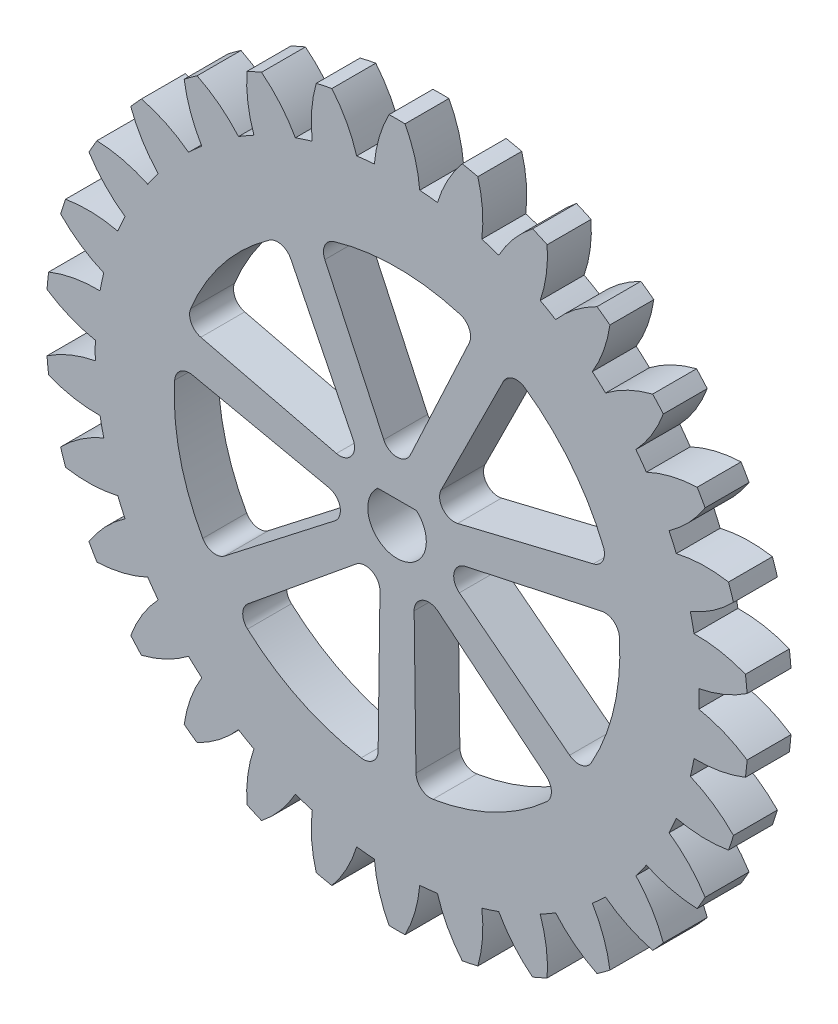
SolidWorks part; units mm, degrees
ref_plane "Front Plane" through (0, 0, 0) normal (0, 0, 1) x (1, 0, 0)
ref_plane "Top Plane" through (0, 0, 0) normal (0, 1, 0) x (1, 0, 0)
ref_plane "Right Plane" through (0, 0, 0) normal (1, 0, 0) x (0, 0, -1)
sketch "Sketch1" plane through (0, 0, 0) normal (0, 0, 1) x (1, 0, 0)
  circle A0 centre (0, 0) radius 24
  dimension "D1" = 48
extrude "Boss-Extrude1" add sketch "Sketch1" along normal blind 3
sketch "Sketch2" plane through (0, 0, 0) normal (0, 0, -1) x (-1, 0, 0)
  line L0 (0, 0) -> (0, 31.1786) construction
  line L1 (0, 0) -> (3.3147, 31.5373) construction
  line L2 (1.1781, 22.4691) -> (0, 22.4691) construction
  circle A0 centre (0, 0) radius 20.625 construction
  circle A1 centre (0, 0) radius 21.1431 construction
  circle A2 centre (0, 0) radius 22.5 construction
  arc A3 (1.5504, 20.5666) -> (2.7595, 20.4396) centre (0, 0) cw
  arc A4 (1.5504, 20.5666) -> (0.5461, 23.9938) centre (-7.4168, 19.7995) ccw
  circle A5 centre (0, 0) radius 24 construction
  arc A6 (2.7595, 20.4396) -> (4.4545, 23.583) centre (11.3713, 17.8248) cw
  arc A7 (0.5461, 23.9938) -> (4.4545, 23.583) centre (0, 0) cw
  dimension "D3" = 45
  dimension "D1" = 41.25
  dimension "D5" = 9
  dimension "D2" = 42.2862
  dimension "D4" = 6
  dimension "D6" = 1.1781
extrude "Cut-Extrude1" cut sketch "Sketch2" against normal through all
pattern_circular "CirPattern1" count 30 over 360 about axis through (0, 0, 0) along (0, 0, 1) of "Cut-Extrude1"
sketch "Sketch4" plane through (0, 0, 0) normal (0, 0, -1) x (-1, 0, 0)
  line L0 (0, 2.6286) -> (5.4036, 14.2321)
  line L1 (0, 2.6286) -> (-5.4036, 14.2321)
  line L2 (0, 0) -> (0, 15.2234) construction
  arc A1 (-5.4036, 14.2321) -> (5.4036, 14.2321) centre (0, 0) cw
  circle A2 centre (0, 0) radius 2.6286 construction
  dimension "D1" = 12.8
extrude "Cut-Extrude3" cut sketch "Sketch4" against normal through all
fillet "Fillet6" radius 1 3 edges at (0, 2.6286, 1.5) (-5.4036, 14.2321, 1.5) (5.4036, 14.2321, 1.5)
pattern_circular "CirPattern3" count 7 over 360 about axis through (0, 0, 0) along (0, 0, 1) of "Fillet6", "Cut-Extrude3"
sketch "Sketch5" plane through (0, 0, 0) normal (0, 0, -1) x (-1, 0, 0)
  line L1 (-1.3229, 1.5) -> (1.3229, 1.5)
  arc A1 (-1.3229, 1.5) -> (1.3229, 1.5) centre (0, 0) ccw
  dimension "D1" = 1.5
  dimension "D2" = 2
extrude "Cut-Extrude4" cut sketch "Sketch5" against normal blind 10
equation "\"module\" = 1.5"
equation "\"teeth\"= 30"
equation "\"pressureAngle\"= 20deg"
equation "\"gearThickness\"= 3"
equation "\"addendumFactor\"= 1"
equation "\"dedendumFactor\"= 1.25"
equation "\"pitch\"= 1 / \"module\""
equation "\"pitchDiameter\"= \"teeth\" / \"pitch\""
equation "\"addendum\"= \"addendumFactor\" / \"pitch\""
equation "\"dedendum\"= \"dedendumFactor\" / \"pitch\""
equation "\"D1@Boss-Extrude1\"=\"gearThickness\""
equation "\"D4@Sketch2\"=180/\"teeth\""
equation "\"D3@Sketch2\"=\"pitchDiameter\""
equation "\"D1@Sketch2\"=\"pitchDiameter\"-2*\"dedendum\""
equation "\"D5@Sketch2\"=\"pitchDiameter\"/5"
equation "\"D6@Sketch2\"=pi/2/\"pitch\"/2"
equation "\"D1@Sketch1\"=\"pitchDiameter\"+2*\"addendum\""
equation "\"D2@Sketch2\"=\"pitchDiameter\" * cos ( \"pressureAngle\" )"
equation "\"D1@CirPattern1\"=\"teeth\""
equation "\"D1@Sketch4\"= (\"pitchDiameter\" + 2 * \"addendum\")/3.75"
